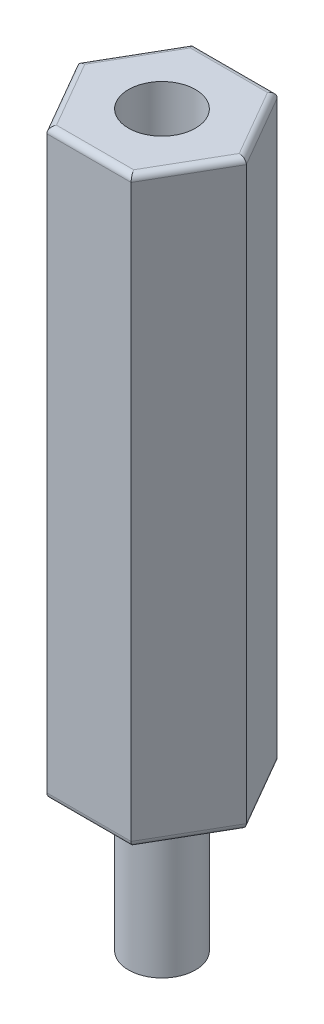
SolidWorks part; units mm, degrees
material "201.0-T43 Molde de fundição com isolamento (SS)"
ref_plane "Plano frontal" through (0, 0, 0) normal (0, 0, 1) x (1, 0, 0)
ref_plane "Plano superior" through (0, 0, 0) normal (0, 1, 0) x (1, 0, 0)
ref_plane "Plano direito" through (0, 0, 0) normal (1, 0, 0) x (0, 0, -1)
sketch "Esboço1" plane through (0, 0, 0) normal (0, 1, 0) x (1, 0, 0)
  line L1 (2.7482, 0) -> (1.3741, 2.38)
  line L2 (1.3741, 2.38) -> (-1.3741, 2.38)
  line L3 (-1.3741, 2.38) -> (-2.7482, 0)
  line L4 (-2.7482, 0) -> (-1.3741, -2.38)
  line L5 (-1.3741, -2.38) -> (1.3741, -2.38)
  line L6 (1.3741, -2.38) -> (2.7482, 0)
  circle A0 centre (0, 0) radius 2.38 construction
  dimension "D1" = 4.76
extrude "Ressalto-extrusão1" add sketch "Esboço1" along normal blind 19
fillet "Filete1" radius 0.2 12 edges at (0, 19, -2.38) (-2.0611, 19, -1.19) (-2.0611, 19, 1.19) (0, 19, 2.38) (2.0611, 19, 1.19) (2.0611, 19, -1.19) (0, 0, 2.38) (-2.0611, 0, 1.19) (-2.0611, 0, -1.19) (0, 0, -2.38) (2.0611, 0, -1.19) (2.0611, 0, 1.19)
sketch "Esboço2" plane through (0, 0, 0) normal (0, -1, 0) x (1, 0, 0)
  circle A0 centre (0, 0) radius 1.0922
  dimension "D1" = 2.1844
extrude "Ressalto-extrusão2" add sketch "Esboço2" along normal blind 4.76
sketch "Esboço3" plane through (0, 19, 0) normal (0, 1, 0) x (1, 0, 0)
  circle A0 centre (0, 0) radius 1.0922
extrude "Corte-extrusão1" cut sketch "Esboço3" against normal blind 4.76
